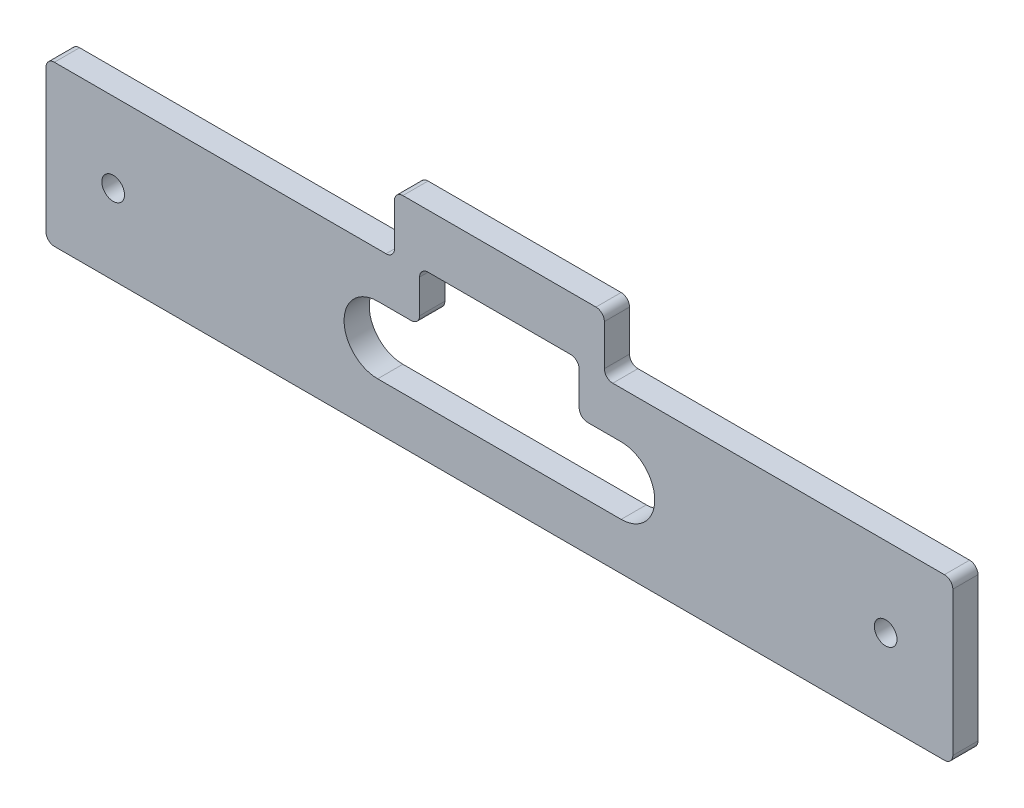
SolidWorks part; units mm, degrees
ref_plane "Plan de face" through (0, 0, 0) normal (0, 0, 1) x (1, 0, 0)
ref_plane "Plan de dessus" through (0, 0, 0) normal (0, 1, 0) x (1, 0, 0)
ref_plane "Plan de droite" through (0, 0, 0) normal (1, 0, 0) x (0, 0, -1)
sketch "Esquisse1" plane through (0, 0, 0) normal (0, 0, 1) x (1, 0, 0)
  line L0 (0, 95) -> (207.5, 95)
  line L1 (0, 0) -> (539.9995, 0)
  line L2 (0, 0) -> (0, 95)
  line L3 (207.5, 95) -> (207.5, 130)
  line L4 (539.9995, 0) -> (539.9995, 95.7315)
  line L5 (207.5, 130) -> (332.5, 130)
  line L6 (332.5, 130) -> (332.5, 95.7315)
  line L7 (332.5, 95.7315) -> (539.9995, 95.7315)
  dimension "D1" = 540
  dimension "D2" = 95
  dimension "D3" = 125
  dimension "D4" = 207.5
  dimension "D5" = 130
extrude "Boss.-Extru.1" add sketch "Esquisse1" along normal blind 15
hole_wizard "Dégagement M121" positions "Esquisse19" profile "Esquisse18" hole size "M12" standard "ISO" end condition through all
sketch "Esquisse19" plane through (0, 0, 0) normal (0, 0, -1) x (-1, 0, 0)
  line L0 (0, 95) -> (0, 0) construction
  line L1 (-539.9995, 0) -> (-539.9995, 95.7315) construction
  line L2 (0, 0) -> (-539.9995, 0) construction
  line L3 (-539.9995, 95.7315) -> (-332.5, 95.7315) construction
  point P0 (-40, 47.5)
  point P2 (-499.9995, 48.2315)
  point P7 (-539.9995, 47.8657)
  dimension "D1" = 40
  dimension "D2" = 40
  dimension "D3" = 47.5
  dimension "D4" = 47.5
sketch "Esquisse18" plane through (40, 47.5, 0) normal (1, 0, 0) x (0, 1, 0)
  line L0 (0, 0) -> (0, 15)
  line L1 (0, 15) -> (6.75, 15)
  line L2 (6.75, 15) -> (6.75, 0)
  line L5 (6.75, 0) -> (0, 0)
  line L11 (0, -6.35) -> (0, 107.95) construction
  dimension "Diamètre du perçage jusqu'au prochain" = 13.5
  dimension "Profondeur du perçage jusqu'au prochain" = 15
sketch "Esquisse20" plane through (0, 0, 0) normal (0, 0, -1) x (-1, 0, 0)
  line L0 (-197.4995, 28) -> (-342.4995, 28)
  line L1 (0, 0) -> (-539.9995, 0) construction
  line L2 (-342.4995, 68) -> (-317.4995, 68)
  line L3 (-317.4995, 68) -> (-317.4995, 98)
  line L4 (-317.4995, 98) -> (-222.4995, 98)
  line L5 (-222.4995, 98) -> (-222.4995, 68)
  line L6 (-222.4995, 68) -> (-197.4995, 68)
  line L7 (-539.9995, 0) -> (-539.9995, 95.7315) construction
  arc A0 (-197.4995, 68) -> (-197.4995, 28) centre (-197.4995, 48) cw
  arc A1 (-342.4995, 68) -> (-342.4995, 28) centre (-342.4995, 48) ccw
  dimension "D1" = 20
  dimension "D2" = 20
  dimension "D6" = 145
  dimension "D7" = 197.5
  dimension "D3" = 70
  dimension "D4" = 95
  dimension "D5" = 28
  dimension "D8" = 222.5
extrude "Enlèv. mat.-Extru.8" cut sketch "Esquisse20" against normal blind 33
fillet "Congé1" radius 5 4 edges at (332.5, 95.7315, 7.5) (332.5, 130, 7.5) (207.5, 130, 7.5) (207.5, 95, 7.5)
fillet "Congé2" radius 5 4 edges at (317.4995, 68, 7.5) (222.4995, 68, 7.5) (317.4995, 98, 7.5) (222.4995, 98, 7.5)
fillet "Congé3" radius 5 4 edges at (0, 95, 7.5) (0, 0, 7.5) (539.9995, 0, 7.5) (539.9995, 95.7315, 7.5)
